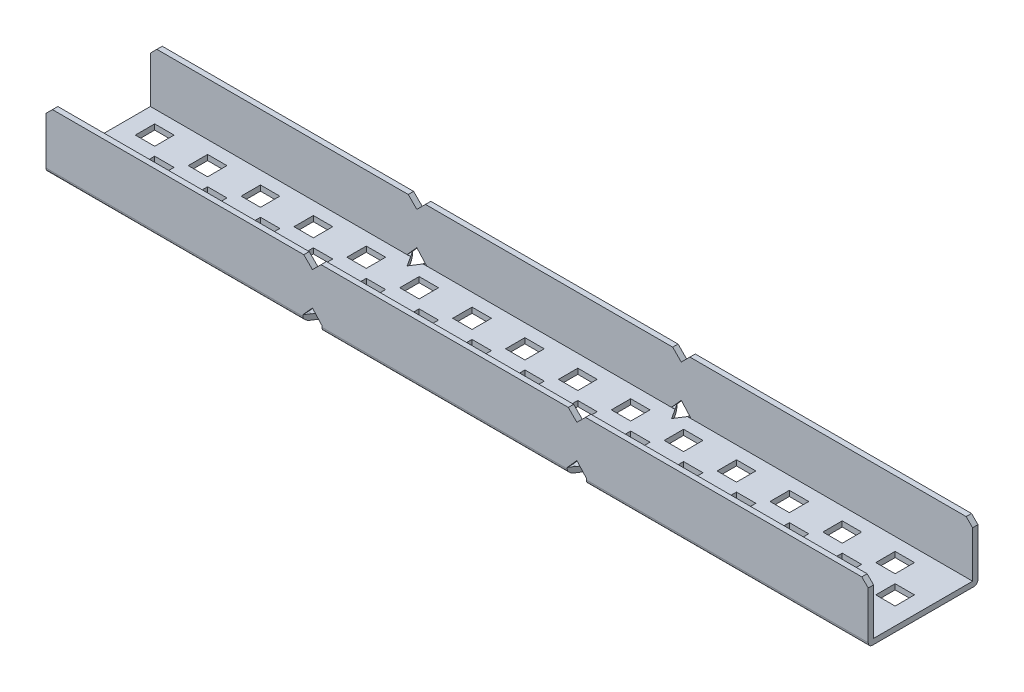
SolidWorks part; units mm, degrees
ref_plane "Front Plane" through (0, 0, 0) normal (0, 0, 1) x (1, 0, 0)
ref_plane "Top Plane" through (0, 0, 0) normal (0, 1, 0) x (1, 0, 0)
ref_plane "Right Plane" through (0, 0, 0) normal (1, 0, 0) x (0, 0, -1)
sketch "Sketch1" plane through (0, 0, 0) normal (0, 1, 0) x (1, 0, 0)
  line L1 (0, 0) -> (191, 0)
  line L2 (0, 0) -> (0, 25.5)
  line L3 (0, 25.5) -> (191, 25.5)
  line L4 (191, 0) -> (191, 25.5)
  dimension "D1" = 25.5
  dimension "D2" = 191
extrude "Boss-Extrude1" add sketch "Sketch1" along normal blind 1.25
sketch "Sketch2" plane through (0, 1.25, 0) normal (0, 1, 0) x (1, 0, 0)
  line L0 (191, 0) -> (191, 25.5) construction
  line L1 (0, 25.5) -> (191, 25.5)
  line L2 (0, 25.5) -> (0, 24.25)
  line L3 (0, 24.25) -> (191, 24.25)
  line L4 (191, 25.5) -> (191, 24.25)
  line L5 (0, 25.5) -> (0, 0) construction
  line L6 (191, 0) -> (0, 0)
  line L7 (191, 0) -> (191, 1.25)
  line L8 (191, 1.25) -> (0, 1.25)
  line L9 (0, 0) -> (0, 1.25)
  dimension "D1" = 1.25
  dimension "D2" = 1.25
extrude "Boss-Extrude2" add sketch "Sketch2" along normal blind 12.25
sketch "Sketch3" plane through (0, 0, 0) normal (0, -1, 0) x (-1, 0, 0)
  line L0 (0, 25.5) -> (0, 0) construction
  line L1 (-4, 4.25) -> (-8.5, 4.25)
  line L2 (-4, 4.25) -> (-4, 8.75)
  line L3 (-4, 8.75) -> (-8.5, 8.75)
  line L4 (-8.5, 4.25) -> (-8.5, 8.75)
  line L5 (-4, 16.75) -> (-8.5, 16.75)
  line L6 (-4, 16.75) -> (-4, 21.25)
  line L7 (-4, 21.25) -> (-8.5, 21.25)
  line L8 (-8.5, 16.75) -> (-8.5, 21.25)
  line L9 (-191, 25.5) -> (0, 25.5) construction
  line L10 (-16.2857, 4.25) -> (-20.7857, 4.25)
  line L11 (-10.5, 10.25) -> (-15, 10.25)
  line L12 (-10.5, 10.25) -> (-10.5, 14.75)
  line L13 (-10.5, 14.75) -> (-15, 14.75)
  line L14 (-15, 10.25) -> (-15, 14.75)
  line L15 (-16.2857, 4.25) -> (-16.2857, 8.75)
  line L16 (-16.2857, 8.75) -> (-20.7857, 8.75)
  line L17 (-20.7857, 4.25) -> (-20.7857, 8.75)
  line L18 (-16.2857, 16.75) -> (-20.7857, 16.75)
  line L19 (-16.2857, 16.75) -> (-16.2857, 21.25)
  line L20 (-16.2857, 21.25) -> (-20.7857, 21.25)
  line L21 (-20.7857, 16.75) -> (-20.7857, 21.25)
  line L22 (-22.7857, 10.25) -> (-27.2857, 10.25)
  line L23 (-22.7857, 10.25) -> (-22.7857, 14.75)
  line L24 (-22.7857, 14.75) -> (-27.2857, 14.75)
  line L25 (-27.2857, 10.25) -> (-27.2857, 14.75)
  line L26 (-28.5714, 4.25) -> (-33.0714, 4.25)
  line L27 (-28.5714, 4.25) -> (-28.5714, 8.75)
  line L28 (-28.5714, 8.75) -> (-33.0714, 8.75)
  line L29 (-33.0714, 4.25) -> (-33.0714, 8.75)
  line L30 (-28.5714, 16.75) -> (-33.0714, 16.75)
  line L31 (-28.5714, 16.75) -> (-28.5714, 21.25)
  line L32 (-28.5714, 21.25) -> (-33.0714, 21.25)
  line L33 (-33.0714, 16.75) -> (-33.0714, 21.25)
  line L34 (-35.0714, 10.25) -> (-39.5714, 10.25)
  line L35 (-35.0714, 10.25) -> (-35.0714, 14.75)
  line L36 (-35.0714, 14.75) -> (-39.5714, 14.75)
  line L37 (-39.5714, 10.25) -> (-39.5714, 14.75)
  line L38 (-40.8571, 4.25) -> (-45.3571, 4.25)
  line L39 (-40.8571, 4.25) -> (-40.8571, 8.75)
  line L40 (-40.8571, 8.75) -> (-45.3571, 8.75)
  line L41 (-45.3571, 4.25) -> (-45.3571, 8.75)
  line L42 (-40.8571, 16.75) -> (-45.3571, 16.75)
  line L43 (-40.8571, 16.75) -> (-40.8571, 21.25)
  line L44 (-40.8571, 21.25) -> (-45.3571, 21.25)
  line L45 (-45.3571, 16.75) -> (-45.3571, 21.25)
  line L46 (-47.3571, 10.25) -> (-51.8571, 10.25)
  line L47 (-47.3571, 10.25) -> (-47.3571, 14.75)
  line L48 (-47.3571, 14.75) -> (-51.8571, 14.75)
  line L49 (-51.8571, 10.25) -> (-51.8571, 14.75)
  line L50 (-53.1429, 4.25) -> (-57.6429, 4.25)
  line L51 (-53.1429, 4.25) -> (-53.1429, 8.75)
  line L52 (-53.1429, 8.75) -> (-57.6429, 8.75)
  line L53 (-57.6429, 4.25) -> (-57.6429, 8.75)
  line L54 (-53.1429, 16.75) -> (-57.6429, 16.75)
  line L55 (-53.1429, 16.75) -> (-53.1429, 21.25)
  line L56 (-53.1429, 21.25) -> (-57.6429, 21.25)
  line L57 (-57.6429, 16.75) -> (-57.6429, 21.25)
  line L58 (-59.6429, 10.25) -> (-64.1429, 10.25)
  line L59 (-59.6429, 10.25) -> (-59.6429, 14.75)
  line L60 (-59.6429, 14.75) -> (-64.1429, 14.75)
  line L61 (-64.1429, 10.25) -> (-64.1429, 14.75)
  line L62 (-65.4286, 4.25) -> (-69.9286, 4.25)
  line L63 (-65.4286, 4.25) -> (-65.4286, 8.75)
  line L64 (-65.4286, 8.75) -> (-69.9286, 8.75)
  line L65 (-69.9286, 4.25) -> (-69.9286, 8.75)
  line L66 (-65.4286, 16.75) -> (-69.9286, 16.75)
  line L67 (-65.4286, 16.75) -> (-65.4286, 21.25)
  line L68 (-65.4286, 21.25) -> (-69.9286, 21.25)
  line L69 (-69.9286, 16.75) -> (-69.9286, 21.25)
  line L70 (-71.9286, 10.25) -> (-76.4286, 10.25)
  line L71 (-71.9286, 10.25) -> (-71.9286, 14.75)
  line L72 (-71.9286, 14.75) -> (-76.4286, 14.75)
  line L73 (-76.4286, 10.25) -> (-76.4286, 14.75)
  line L74 (-77.7143, 4.25) -> (-82.2143, 4.25)
  line L75 (-77.7143, 4.25) -> (-77.7143, 8.75)
  line L76 (-77.7143, 8.75) -> (-82.2143, 8.75)
  line L77 (-82.2143, 4.25) -> (-82.2143, 8.75)
  line L78 (-77.7143, 16.75) -> (-82.2143, 16.75)
  line L79 (-77.7143, 16.75) -> (-77.7143, 21.25)
  line L80 (-77.7143, 21.25) -> (-82.2143, 21.25)
  line L81 (-82.2143, 16.75) -> (-82.2143, 21.25)
  line L82 (-84.2143, 10.25) -> (-88.7143, 10.25)
  line L83 (-84.2143, 10.25) -> (-84.2143, 14.75)
  line L84 (-84.2143, 14.75) -> (-88.7143, 14.75)
  line L85 (-88.7143, 10.25) -> (-88.7143, 14.75)
  line L86 (-90, 4.25) -> (-94.5, 4.25)
  line L87 (-90, 4.25) -> (-90, 8.75)
  line L88 (-90, 8.75) -> (-94.5, 8.75)
  line L89 (-94.5, 4.25) -> (-94.5, 8.75)
  line L90 (-90, 16.75) -> (-94.5, 16.75)
  line L91 (-90, 16.75) -> (-90, 21.25)
  line L92 (-90, 21.25) -> (-94.5, 21.25)
  line L93 (-94.5, 16.75) -> (-94.5, 21.25)
  line L94 (-96.5, 10.25) -> (-101, 10.25)
  line L95 (-96.5, 10.25) -> (-96.5, 14.75)
  line L96 (-96.5, 14.75) -> (-101, 14.75)
  line L97 (-101, 10.25) -> (-101, 14.75)
  line L98 (-102.2857, 4.25) -> (-106.7857, 4.25)
  line L99 (-102.2857, 4.25) -> (-102.2857, 8.75)
  line L100 (-102.2857, 8.75) -> (-106.7857, 8.75)
  line L101 (-106.7857, 4.25) -> (-106.7857, 8.75)
  line L102 (-102.2857, 16.75) -> (-106.7857, 16.75)
  line L103 (-102.2857, 16.75) -> (-102.2857, 21.25)
  line L104 (-102.2857, 21.25) -> (-106.7857, 21.25)
  line L105 (-106.7857, 16.75) -> (-106.7857, 21.25)
  line L106 (-108.7857, 10.25) -> (-113.2857, 10.25)
  line L107 (-108.7857, 10.25) -> (-108.7857, 14.75)
  line L108 (-108.7857, 14.75) -> (-113.2857, 14.75)
  line L109 (-113.2857, 10.25) -> (-113.2857, 14.75)
  line L110 (-114.5714, 4.25) -> (-119.0714, 4.25)
  line L111 (-114.5714, 4.25) -> (-114.5714, 8.75)
  line L112 (-114.5714, 8.75) -> (-119.0714, 8.75)
  line L113 (-119.0714, 4.25) -> (-119.0714, 8.75)
  line L114 (-114.5714, 16.75) -> (-119.0714, 16.75)
  line L115 (-114.5714, 16.75) -> (-114.5714, 21.25)
  line L116 (-114.5714, 21.25) -> (-119.0714, 21.25)
  line L117 (-119.0714, 16.75) -> (-119.0714, 21.25)
  line L118 (-121.0714, 10.25) -> (-125.5714, 10.25)
  line L119 (-121.0714, 10.25) -> (-121.0714, 14.75)
  line L120 (-121.0714, 14.75) -> (-125.5714, 14.75)
  line L121 (-125.5714, 10.25) -> (-125.5714, 14.75)
  line L122 (-126.8571, 4.25) -> (-131.3571, 4.25)
  line L123 (-126.8571, 4.25) -> (-126.8571, 8.75)
  line L124 (-126.8571, 8.75) -> (-131.3571, 8.75)
  line L125 (-131.3571, 4.25) -> (-131.3571, 8.75)
  line L126 (-126.8571, 16.75) -> (-131.3571, 16.75)
  line L127 (-126.8571, 16.75) -> (-126.8571, 21.25)
  line L128 (-126.8571, 21.25) -> (-131.3571, 21.25)
  line L129 (-131.3571, 16.75) -> (-131.3571, 21.25)
  line L130 (-133.3571, 10.25) -> (-137.8571, 10.25)
  line L131 (-133.3571, 10.25) -> (-133.3571, 14.75)
  line L132 (-133.3571, 14.75) -> (-137.8571, 14.75)
  line L133 (-137.8571, 10.25) -> (-137.8571, 14.75)
  line L134 (-139.1429, 4.25) -> (-143.6429, 4.25)
  line L135 (-139.1429, 4.25) -> (-139.1429, 8.75)
  line L136 (-139.1429, 8.75) -> (-143.6429, 8.75)
  line L137 (-143.6429, 4.25) -> (-143.6429, 8.75)
  line L138 (-139.1429, 16.75) -> (-143.6429, 16.75)
  line L139 (-139.1429, 16.75) -> (-139.1429, 21.25)
  line L140 (-139.1429, 21.25) -> (-143.6429, 21.25)
  line L141 (-143.6429, 16.75) -> (-143.6429, 21.25)
  line L142 (-145.6429, 10.25) -> (-150.1429, 10.25)
  line L143 (-145.6429, 10.25) -> (-145.6429, 14.75)
  line L144 (-145.6429, 14.75) -> (-150.1429, 14.75)
  line L145 (-150.1429, 10.25) -> (-150.1429, 14.75)
  line L146 (-151.4286, 4.25) -> (-155.9286, 4.25)
  line L147 (-151.4286, 4.25) -> (-151.4286, 8.75)
  line L148 (-151.4286, 8.75) -> (-155.9286, 8.75)
  line L149 (-155.9286, 4.25) -> (-155.9286, 8.75)
  line L150 (-151.4286, 16.75) -> (-155.9286, 16.75)
  line L151 (-151.4286, 16.75) -> (-151.4286, 21.25)
  line L152 (-151.4286, 21.25) -> (-155.9286, 21.25)
  line L153 (-155.9286, 16.75) -> (-155.9286, 21.25)
  line L154 (-157.9286, 10.25) -> (-162.4286, 10.25)
  line L155 (-157.9286, 10.25) -> (-157.9286, 14.75)
  line L156 (-157.9286, 14.75) -> (-162.4286, 14.75)
  line L157 (-162.4286, 10.25) -> (-162.4286, 14.75)
  line L158 (-163.7143, 4.25) -> (-168.2143, 4.25)
  line L159 (-163.7143, 4.25) -> (-163.7143, 8.75)
  line L160 (-163.7143, 8.75) -> (-168.2143, 8.75)
  line L161 (-168.2143, 4.25) -> (-168.2143, 8.75)
  line L162 (-163.7143, 16.75) -> (-168.2143, 16.75)
  line L163 (-163.7143, 16.75) -> (-163.7143, 21.25)
  line L164 (-163.7143, 21.25) -> (-168.2143, 21.25)
  line L165 (-168.2143, 16.75) -> (-168.2143, 21.25)
  line L166 (-170.2143, 10.25) -> (-174.7143, 10.25)
  line L167 (-170.2143, 10.25) -> (-170.2143, 14.75)
  line L168 (-170.2143, 14.75) -> (-174.7143, 14.75)
  line L169 (-174.7143, 10.25) -> (-174.7143, 14.75)
  line L170 (-176, 4.25) -> (-180.5, 4.25)
  line L171 (-176, 4.25) -> (-176, 8.75)
  line L172 (-176, 8.75) -> (-180.5, 8.75)
  line L173 (-180.5, 4.25) -> (-180.5, 8.75)
  line L174 (-176, 16.75) -> (-180.5, 16.75)
  line L175 (-176, 16.75) -> (-176, 21.25)
  line L176 (-176, 21.25) -> (-180.5, 21.25)
  line L177 (-180.5, 16.75) -> (-180.5, 21.25)
  line L178 (-182.5, 10.25) -> (-187, 10.25)
  line L179 (-182.5, 10.25) -> (-182.5, 14.75)
  line L180 (-182.5, 14.75) -> (-187, 14.75)
  line L181 (-187, 10.25) -> (-187, 14.75)
  line L182 (-191, 0) -> (-191, 25.5) construction
  dimension "D1" = 4.5
  dimension "D2" = 4
  dimension "D3" = 8
  dimension "D4" = 4.25
  dimension "D5" = 2
  dimension "D6" = 2
  dimension "D8" = 4
  dimension "D7" = 15
extrude "Cut-Extrude1" cut sketch "Sketch3" against normal blind 12.25
sketch "Sketch4" plane through (0, 0, 0) normal (0, -1, 0) x (1, 0, 0)
  line L0 (61.8929, -3.5) -> (59.6429, 0)
  line L1 (0, 0) -> (191, 0) construction
  line L2 (61.8929, -3.5) -> (64.1429, 0)
  line L3 (59.6429, 0) -> (64.1429, 0)
  line L4 (64.1429, -10.25) -> (59.6429, -10.25) construction
  line L6 (123.3214, -3.5) -> (121.0714, 0)
  line L7 (121.0714, 0) -> (125.5714, 0)
  line L8 (123.3214, -3.5) -> (125.5714, 0)
  line L9 (125.5714, -10.25) -> (121.0714, -10.25) construction
  line L10 (0, -12.75) -> (219.3109, -12.75) construction
  line L12 (121.0714, -25.5) -> (125.5714, -25.5)
  line L13 (123.3214, -22) -> (125.5714, -25.5)
  line L14 (123.3214, -22) -> (121.0714, -25.5)
  line L15 (59.6429, -25.5) -> (64.1429, -25.5)
  line L16 (61.8929, -22) -> (59.6429, -25.5)
  line L17 (61.8929, -22) -> (64.1429, -25.5)
  line L18 (4, -16.75) -> (4, -21.25) construction
  line L19 (47.3571, -14.75) -> (51.8571, -14.75) construction
  point P0 (61.8929, 0)
  point P8 (61.8929, -10.25)
  point P15 (123.3214, -10.25)
  dimension "D1" = 4.5
  dimension "D2" = 3.5
  dimension "D3" = 2
  dimension "D4" = 47.8571
  dimension "D5" = 2
  dimension "D6" = 7.25
extrude "Cut-Extrude2" cut sketch "Sketch4" against normal blind 1.3
sketch "Sketch6" plane through (0, 0, -25.5) normal (0, 0, -1) x (-1, 0, 0)
  line L0 (-125.5714, 1.3) -> (-123.3214, 3.8)
  line L1 (-123.3214, 3.8) -> (-121.0714, 1.3)
  line L2 (-125.5714, 0) -> (-121.0714, 0)
  line L3 (-125.5714, 1.3) -> (-121.0714, 1.3)
  line L4 (-64.1429, 1.3) -> (-61.8929, 3.8)
  line L5 (-61.8929, 3.8) -> (-59.6429, 1.3)
  line L6 (-64.1429, 1.3) -> (-59.6429, 1.3)
  line L8 (-125.3214, 13.5) -> (-121.3214, 13.5)
  line L9 (-125.3214, 13.5) -> (-123.3214, 11.5)
  line L10 (-191, 13.5) -> (0, 13.5) construction
  line L11 (-123.3214, 11.5) -> (-121.3214, 13.5)
  line L12 (-63.8929, 13.5) -> (-61.8929, 11.5)
  line L13 (-61.8929, 11.5) -> (-59.8929, 13.5)
  line L14 (-63.8929, 13.5) -> (-59.8929, 13.5)
  point P7 (0, 0)
  point P24 (0, 0)
  point P26 (0, 0)
  point P27 (-121.8297, 13.5)
  point P28 (0, 0)
  point P29 (-123.3214, 13.5)
  point P30 (0, 0)
  point P31 (-61.8929, 13.5)
  point P32 (0, 0)
  point P33 (0, 0)
  point P34 (0, 0)
  line M2 (-125.5714, 1.3) -> (-121.0714, 1.3)
  line M6 (-64.1429, 1.3) -> (-59.6429, 1.3)
  dimension "D1" = 2.5
  dimension "D3" = 4
  dimension "D4" = 4
  dimension "D5" = 2
  dimension "D2" = 2
extrude "Cut-Extrude4" cut sketch "Sketch6" against normal blind 48.3 contours L1 L0 M2 | L5 L4 M6 | L8 L11 L9 | L14 L13 L12
sketch "Sketch7" plane through (0, 0, -25.5) normal (0, 0, -1) x (-1, 0, 0)
  line L0 (-191, 13.5) -> (-191, 12)
  line L1 (-191, 13.5) -> (-191, 0) construction
  line L2 (-191, 12) -> (-189.5, 13.5)
  line L3 (-191, 13.5) -> (-125.3214, 13.5) construction
  line L4 (-189.5, 13.5) -> (-191, 13.5)
  line L5 (-1.5, 13.5) -> (0, 13.5)
  line L6 (-59.8929, 13.5) -> (0, 13.5) construction
  line L7 (0, 13.5) -> (0, 12)
  line L8 (0, 13.5) -> (0, 0) construction
  line L9 (0, 12) -> (-1.5, 13.5)
  dimension "D1" = 1.5
  dimension "D2" = 1.5
  dimension "D3" = 1.5
  dimension "D4" = 1.5
extrude "Cut-Extrude5" cut sketch "Sketch7" against normal blind 48.3
fillet "Fillet1" radius 1 6 edges at (158.2857, 0, 0) (92.6071, 0, 0) (29.8214, 0, 0) (29.8214, 0, -25.5) (92.6071, 0, -25.5) (158.2857, 0, -25.5)
